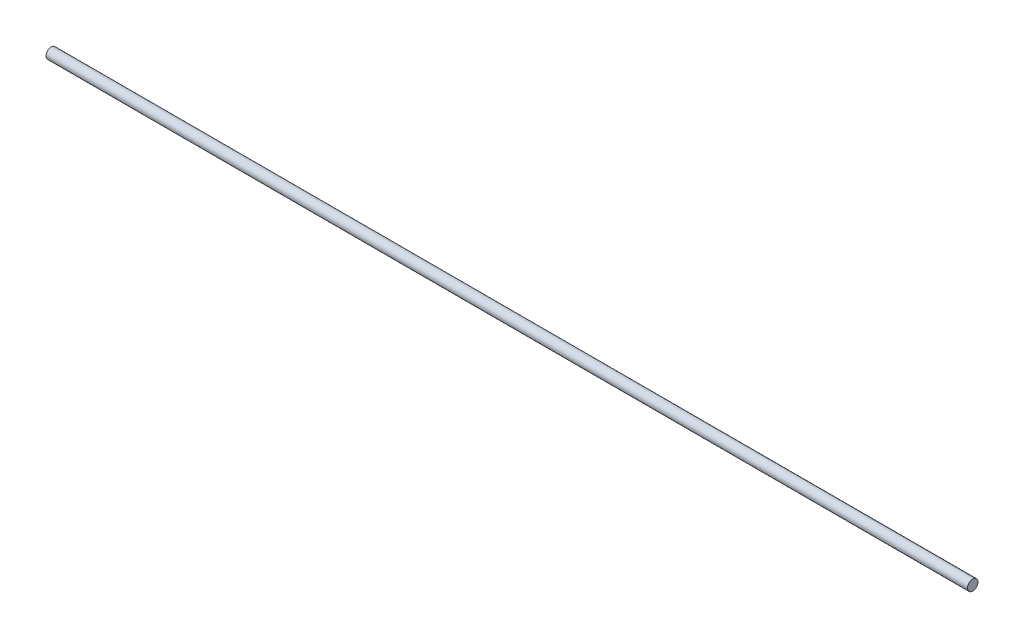
SolidWorks part; units mm, degrees
ref_plane "Alzado" through (0, 0, 0) normal (0, 0, 1) x (1, 0, 0)
ref_plane "Planta" through (0, 0, 0) normal (0, 1, 0) x (1, 0, 0)
ref_plane "Vista lateral" through (0, 0, 0) normal (1, 0, 0) x (0, 0, -1)
sketch "Croquis1" plane through (0, 0, 0) normal (0, 0, 1) x (1, 0, 0)
  line L0 (0, 0) -> (550, 0)
  dimension "D1" = 550
sweep "Barrer1" add path "Croquis1" circular profile diameter 6.25 parameters "D3"=6.25
